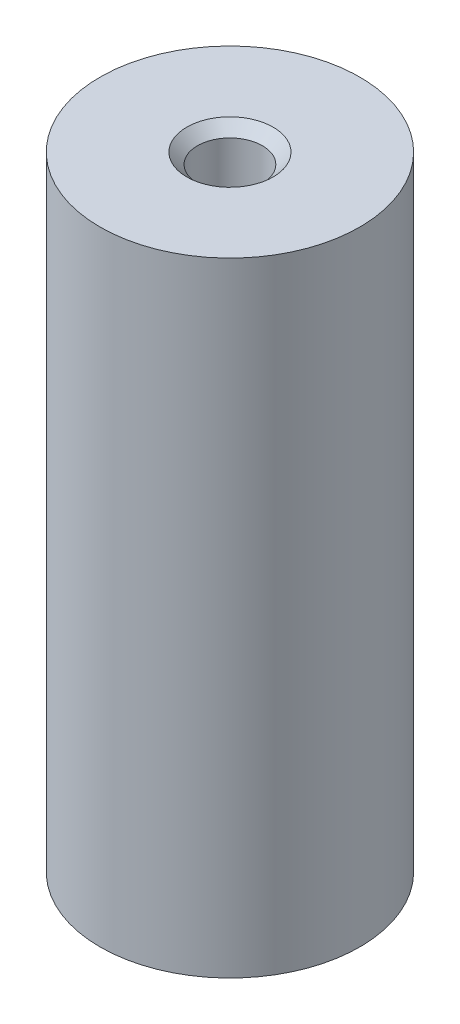
SolidWorks part; units mm, degrees
ref_plane "前视基准面" through (0, 0, 0) normal (0, 0, 1) x (1, 0, 0)
ref_plane "上视基准面" through (0, 0, 0) normal (0, 1, 0) x (1, 0, 0)
ref_plane "右视基准面" through (0, 0, 0) normal (1, 0, 0) x (0, 0, -1)
sketch "草图1" plane through (0, 0, 0) normal (0, 1, 0) x (1, 0, 0)
  circle A0 centre (0, 0) radius 10
  dimension "D1" = 20
extrude "凸台-拉伸1" add sketch "草图1" along normal blind 48
hole_wizard "M6 螺纹孔1" positions "3D草图1" profile "草图2" tap size "M6" standard "GB"
sketch3d "3D草图1"
  line L0 (0, 48, 0) -> (0, 0, 0) construction
  point P0 (0, 48, 0)
sketch "草图2" plane through (0, 48, 0) normal (1, 0, 0) x (0, 0, 1)
  line L0 (0, 0) -> (0, 18.5022)
  line L1 (0, 18.5022) -> (2.5, 17)
  line L2 (2.5, 17) -> (2.5, 0.825)
  line L3 (2.5, 0.825) -> (3.325, 0)
  line L5 (3.325, 0) -> (0, 0)
  line L6 (-2.5, 0.825) -> (-3.325, 0) construction
  line L10 (0, 18.5022) -> (-2.5, 17) construction
  line L11 (0, -6.35) -> (0, 107.95) construction
  dimension "螺纹孔钻头直径" = 5
  dimension "螺纹孔钻头深度" = 17
  dimension "近端锥形沉头孔直径" = 6.65
  dimension "近端锥形沉头孔角度" = 90
  dimension "导头角度" = 118
cosmetic thread "孔螺蚊线1" parameters "D1"=12, "D2"=6
